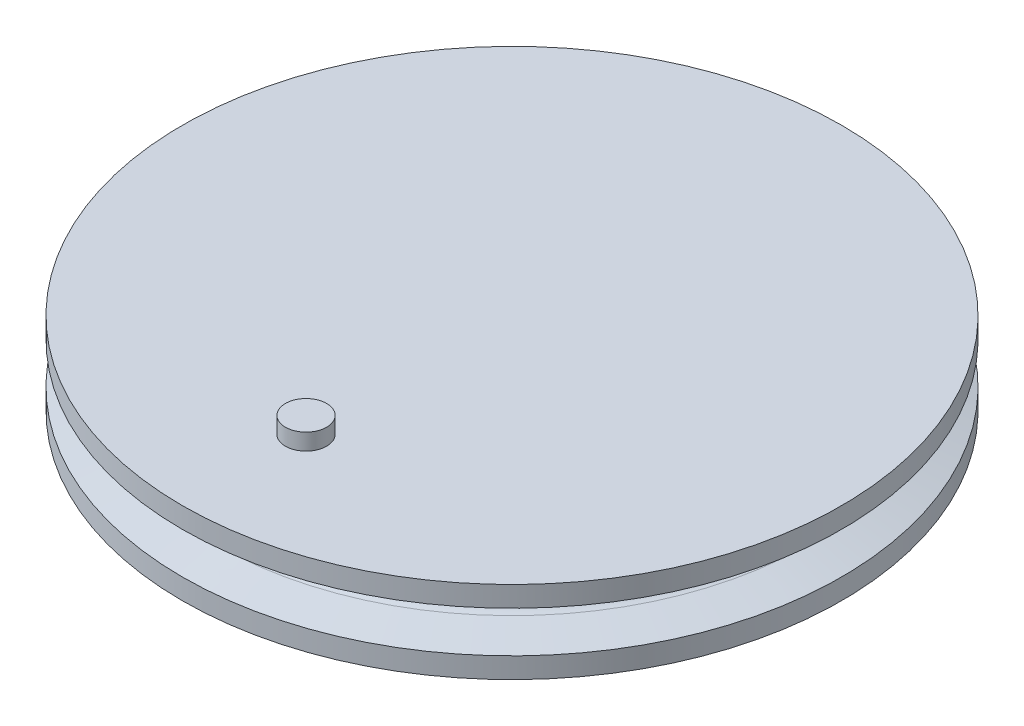
SolidWorks part; units mm, degrees
ref_plane "Front Plane" through (0, 0, 0) normal (0, 0, 1) x (1, 0, 0)
ref_plane "Top Plane" through (0, 0, 0) normal (0, 1, 0) x (1, 0, 0)
ref_plane "Right Plane" through (0, 0, 0) normal (1, 0, 0) x (0, 0, -1)
sketch "Sketch1" plane through (0, 0, 0) normal (0, 1, 0) x (1, 0, 0)
  circle A0 centre (0, 0) radius 35
  dimension "D1" = 70
extrude "Boss-Extrude1" add sketch "Sketch1" along normal blind 10
ref_axis "Axis1" through (0, 10, 0) along (0, -1, 0)
sketch "Sketch2" plane through (0, 0, 0) normal (1, 0, 0) x (0, 0, -1)
  line L0 (35, 0) -> (35, 10) construction
  line L1 (35, 10) -> (40, 10)
  line L2 (40, 10) -> (40, 7.5)
  line L3 (40, 7.5) -> (35.8723, 6.1916)
  line L4 (35, 0) -> (40, 0)
  line L5 (40, 0) -> (40, 2.5)
  line L6 (40, 2.5) -> (35.8723, 3.8084)
  line L7 (36.25, 10) -> (36.25, 0) construction
  line L8 (35, 10) -> (34, 10)
  line L9 (35, 10) -> (-35, 10) construction
  line L10 (34, 10) -> (34, 0)
  line L11 (-35, 0) -> (35, 0) construction
  line L12 (34, 0) -> (35, 0)
  arc A0 (35.8723, 6.1916) -> (35.8723, 3.8084) centre (36.25, 5) ccw
  dimension "D1" = 2.5
  dimension "D2" = 2.5
  dimension "D3" = 5
revolve "Revolve1" add sketch "Sketch2" angle 360 about axis through (0, 10, 0) along (0, -1, 0)
sketch "Sketch3" plane through (0, 0, 0) normal (0, -1, 0) x (1, 0, 0)
  circle A0 centre (0, 0) radius 5
  dimension "D1" = 10
extrude "Cut-Extrude1" cut sketch "Sketch3" against normal blind 5
sketch "Sketch4" plane through (0, 10, 0) normal (0, 1, 0) x (1, 0, 0)
  line L0 (0, 0) -> (0, -25) construction
  circle A0 centre (0, -25) radius 2.5
  dimension "D1" = 25
  dimension "D2" = 5
extrude "Boss-Extrude2" add sketch "Sketch4" along normal blind 2
